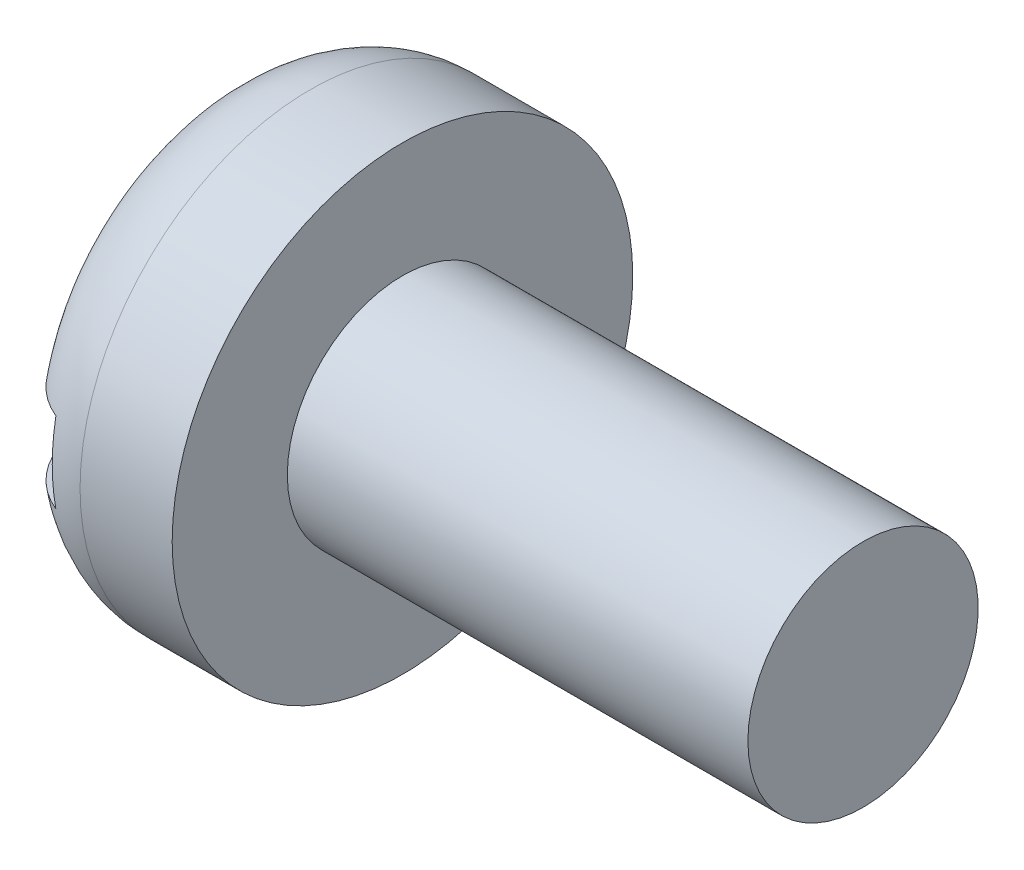
SolidWorks part; units mm, degrees
ref_plane "Plane1" through (0, 0, 0) normal (0, 0, 1) x (1, 0, 0)
ref_plane "Plane2" through (0, 0, 0) normal (0, 1, 0) x (1, 0, 0)
ref_plane "Plane3" through (0, 0, 0) normal (1, 0, 0) x (0, 0, -1)
sketch "BodySke" plane through (0, 0, 0) normal (0, 0, 1) x (1, 0, 0)
  line L0 (1.6, 1) -> (1.6, 2)
  line L1 (0, 0) -> (0, 1.2)
  line L2 (-25.4, 0) -> (127, 0) construction
  line L3 (5.6, 0) -> (0, 0)
  line L4 (1.6, 1) -> (5.6, 1)
  line L5 (5.6, 1) -> (5.6, 0)
  line L6 (0.8, 2) -> (1.6, 2)
  line L7 (1.6, -1) -> (5.6, -1) construction
  line L8 (0, -2) -> (1.6, -2) construction
  line L9 (2, 2.5875) -> (2, -6.9375) construction
  line L10 (1.6, 6.35) -> (1.6, -3.175) construction
  arc A0 (0, 1.2) -> (0.8, 2) centre (0.8, 1.2) cw
  point P15 (0, 2)
  dimension "Head_fillet_rad" = 0.8
  dimension "Head_ht" = 1.6
  dimension "Diameter" = 2
  dimension "Length" = 4
  dimension "Head_dia" = 4
  dimension "Advance" = 0.4
  dimension "Thread_nom" = 4
revolve "Base-Revolve" add sketch "BodySke" angle 360 about L2
cosmetic thread "ThreadCosmetic" [suppressed] parameters "Thread_length"=3.6, "Thread_minor"=1.548
sketch "Sketch2" plane through (0, 0, 0) normal (1, 0, 0) x (0, 0, -1)
  line L0 (2, -0.35) -> (-2, -0.35)
  line L1 (2, -0.35) -> (2, 0.35)
  line L2 (-2, 0.35) -> (2, 0.35)
  line L3 (-2, 0.35) -> (-2, -0.35)
  dimension "D1" = 4
  dimension "D2" = 2
  dimension "Slot_width" = 0.7
  dimension "D3" = 0.35
extrude "Slot" cut sketch "Sketch2" along normal blind 0.5
sketch "ThdSchSke" plane through (0, 0, 0) normal (0, 0, 1) x (1, 0, 0)
  line L0 (2, -0.774) -> (1.8418, -1)
  line L1 (2, -0.774) -> (2.1582, -1)
  line L2 (2.1582, -1) -> (2.1582, -1.25)
  line L3 (-3.175, 0) -> (5.1513, 0) construction
  line L5 (2.1582, -1.25) -> (1.8418, -1.25)
  line L6 (1.8418, -1.25) -> (1.8418, -1)
  dimension "Thread_minor" = 1.548
  dimension "Diameter" = 2
  dimension "Start" = 2
  dimension "SideAngle" = 55
  dimension "VeeAngle" = 70
  dimension "Overcut" = 2.5
revolve "ThreadSchematic" [suppressed] cut sketch "ThdSchSke" angle 360 about L3
pattern_linear "ThdSchPat" [suppressed]
equation "\"D1@Sketch2\" = \"Head_dia@BodySke\""
equation "\"D2@Sketch2\" = \"D1@Sketch2\" / 2"
equation "\"D3@Sketch2\" = \"Slot_width@Sketch2\" / 2"
equation "\"Thread_length@ThreadCosmetic\" = ((sgn( (\"Length@BodySke\" - \"Advance@BodySke\" ) - \"Thread_nom@BodySke\" )-1)*( (\"Length@BodySke\" - \"Advance@BodySke\" ) - \"Thread_nom@BodySke\" ))/-2+ \"Thread_nom@BodySke\""
equation "\"Thread_minor@ThdSchSke\" = \"Thread_minor@ThreadCosmetic\""
equation "\"Diameter@ThdSchSke\" = \"Diameter@BodySke\""
equation "\"Overcut@ThdSchSke\" = \"Diameter@BodySke\" * 1.25"
equation "\"Start@ThdSchSke\" = \"Head_ht@BodySke\" + \"Length@BodySke\" - \"Thread_length@ThreadCosmetic\"  '---Non-countersunk---"
equation "\"Num_threads@ThdSchPat\" = int( \"Thread_length@ThreadCosmetic\" / \"Advance@BodySke\" + 0.999 )  + 1"
equation "\"Advance@ThdSchPat\" = \"Thread_length@ThreadCosmetic\" /  (\"Num_threads@ThdSchPat\" - 1) 'relax it"
